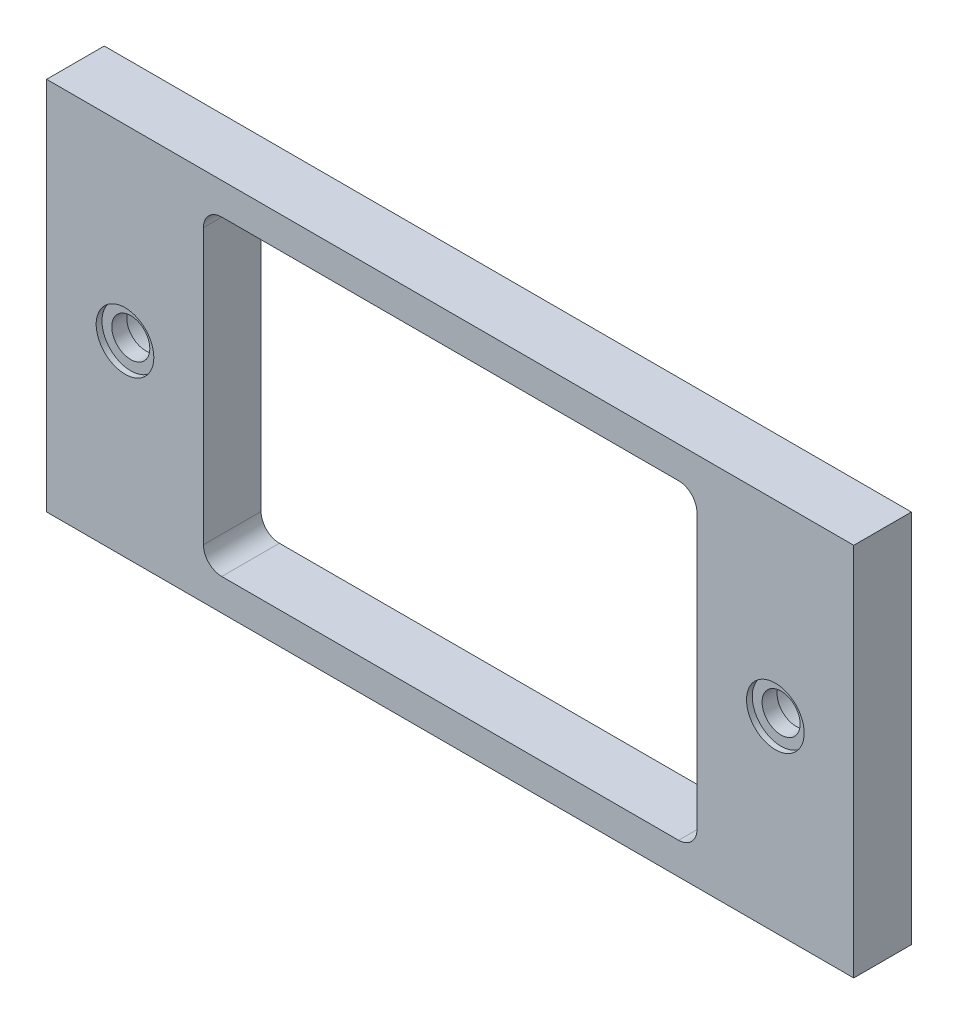
SolidWorks part; units mm, degrees
ref_plane "前视基准面" through (0, 0, 0) normal (0, 0, 1) x (1, 0, 0)
ref_plane "上视基准面" through (0, 0, 0) normal (0, 1, 0) x (1, 0, 0)
ref_plane "右视基准面" through (0, 0, 0) normal (1, 0, 0) x (0, 0, -1)
sketch "草图1" plane through (0, 0, 0) normal (0, 0, 1) x (1, 0, 0)
  line L1 (0, 0) -> (140, 0)
  line L2 (0, 0) -> (0, 65)
  line L3 (0, 65) -> (140, 65)
  line L4 (140, 0) -> (140, 65)
  dimension "D1" = 140
  dimension "D2" = 65
extrude "凸台-拉伸1" add sketch "草图1" along normal blind 10
sketch "草图2" plane through (0, 0, 10) normal (0, 0, 1) x (1, 0, 0)
  line L0 (70, 65) -> (70, 0) construction
  line L1 (140, 65) -> (0, 65) construction
  line L2 (0, 0) -> (140, 0) construction
  line L3 (70, 32.5) -> (140, 32.5) construction
  line L4 (140, 0) -> (140, 65) construction
  line L6 (27.2, 59.5) -> (112.8, 59.5)
  line L7 (27.2, 59.5) -> (27.2, 5.5)
  line L8 (27.2, 5.5) -> (112.8, 5.5)
  line L9 (112.8, 59.5) -> (112.8, 5.5)
  dimension "D1" = 54
  dimension "D2" = 85.6
extrude "切除-拉伸1" cut sketch "草图2" against normal through all
fillet "圆角1" radius 3.18 4 edges at (112.8, 5.5, 5) (27.2, 5.5, 5) (112.8, 59.5, 5) (27.2, 59.5, 5)
hole_wizard "M6 六角凹头螺钉的柱形沉头孔1" positions "草图4" profile "草图5" counterbore size "M6" standard "ISO"
sketch "草图4" plane through (0, 0, 0) normal (0, 0, -1) x (-1, 0, 0)
  line L0 (-112.8, 32.5) -> (-140, 32.5) construction
  line L1 (-112.8, 8.68) -> (-112.8, 56.32) construction
  line L2 (-140, 0) -> (-140, 65) construction
  line L3 (-140, 32.5) -> (-126.4, 32.5) construction
  line L5 (-70, 59.5) -> (-70, 5.5) construction
  line L6 (-109.62, 59.5) -> (-30.38, 59.5) construction
  line L7 (-30.38, 5.5) -> (-109.62, 5.5) construction
  point P0 (-126.4, 32.5)
  point P22 (-13.6, 32.5)
sketch "草图5" plane through (126.4, 32.5, 0) normal (1, 0, 0) x (0, 1, 0)
  line L0 (0, 0) -> (0, 16.9828)
  line L1 (0, 16.9828) -> (3.3, 15)
  line L2 (3.3, 15) -> (3.3, 6.4)
  line L3 (3.3, 6.4) -> (5.5, 6.4)
  line L4 (5.5, 6.4) -> (5.5, 0)
  line L5 (5.5, 0) -> (0, 0)
  line L10 (0, 16.9828) -> (-3.3, 15) construction
  line L11 (0, -6.35) -> (0, 107.95) construction
  dimension "孔直径" = 6.6
  dimension "孔深度" = 15
  dimension "柱形沉头孔直径" = 11
  dimension "柱形沉头孔深度" = 6.4
  dimension "导头角度" = 118
sketch "草图6" plane through (0, 0, 10) normal (0, 0, 1) x (1, 0, 0)
  circle A0 centre (13.6, 32.5) radius 5
  circle A1 centre (126.4, 32.5) radius 5
  dimension "D1" = 10
  dimension "D2" = 10
extrude "切除-拉伸3" cut sketch "草图6" against normal blind 1
